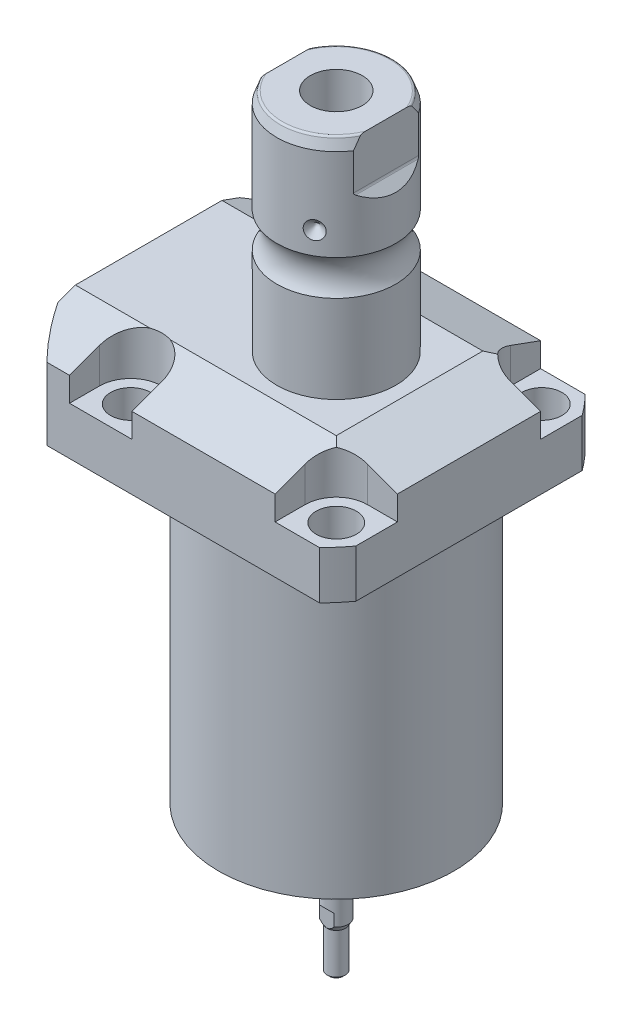
SolidWorks part; units mm, degrees
material "Alloy Steel"
ref_plane "Front Plane" through (0, 0, 0) normal (0, 0, 1) x (1, 0, 0)
ref_plane "Top Plane" through (0, 0, 0) normal (0, 1, 0) x (1, 0, 0)
ref_plane "Right Plane" through (0, 0, 0) normal (1, 0, 0) x (0, 0, -1)
sketch "Sketch1" plane through (0, 0, 0) normal (0, -1, 0) x (0, 0, 1)
  line L0 (-35.433, 50.063) -> (35.433, 50.063)
  line L1 (35.433, 50.063) -> (35.433, -35.433)
  line L2 (35.433, -35.433) -> (-35.433, -35.433)
  line L3 (-35.433, -35.433) -> (-35.433, 50.063)
  line L4 (0, 0) -> (0, -60.6467) construction
  dimension "D1" = 35.433
  dimension "D2" = 85.496
  dimension "D3" = 70.866
extrude "Extrude1" add sketch "Sketch1" against normal blind 104.521
sketch "Sketch2" plane through (0, 0, 0) normal (0, -1, 0) x (1, 0, 0)
  circle A0 centre (-5.4102, 0) radius 50.8
  dimension "D1" = 101.6
  dimension "D2" = 5.4102
extrude "Cut-Extrude1" cut sketch "Sketch2" against normal through all flip side to cut
sketch "Sketch3" plane through (0, 0, 0) normal (1, 0, 0) x (0, 0, -1)
  line L0 (31.3945, 0) -> (31.3945, 79.502)
  line L1 (31.3945, 79.502) -> (76.5937, 79.502)
  line L2 (76.5937, 79.502) -> (76.5937, 0)
  line L3 (76.5937, 0) -> (31.3945, 0)
  line L4 (0, -93.345) -> (0, 4.445) construction
  line L5 (24.2233, 0) -> (-24.2233, 0) construction
  dimension "D1" = 62.789
  dimension "D2" = 153.1874
  dimension "D3" = 79.502
revolve "Cut-Revolve1" cut sketch "Sketch3" angle 360 about L4
fillet "Fillet1" radius 0.381 1 edges at (0, 79.502, -31.3945)
sketch "Sketch4" plane through (0, 104.521, 0) normal (0, 1, 0) x (-1, 0, 0)
  line L0 (-35.433, -30.2072) -> (-35.433, 30.2072) construction
  line L1 (41.8127, 35.433) -> (-30.9923, 35.433) construction
  line L2 (-19.1008, -35.433) -> (-19.1008, -27.432)
  line L3 (-35.433, -35.433) -> (-19.1008, -35.433)
  line L4 (-35.433, -19.1008) -> (-35.433, -35.433)
  line L5 (-27.432, -19.1008) -> (-35.433, -19.1008)
  line L6 (35.7632, -35.433) -> (19.1008, -35.433)
  line L7 (19.1008, 35.433) -> (19.1008, 27.432)
  line L8 (35.7632, 35.433) -> (35.7632, 27.432)
  line L9 (35.7632, 35.433) -> (19.1008, 35.433)
  line L10 (-27.432, 19.1008) -> (-35.433, 19.1008)
  line L11 (-35.433, 19.1008) -> (-35.433, 35.433)
  line L12 (-35.433, 35.433) -> (-19.1008, 35.433)
  line L13 (-19.1008, 35.433) -> (-19.1008, 27.432)
  line L14 (-48.9217, 0) -> (49.4551, 0) construction
  line L15 (35.7632, -35.433) -> (35.7632, -27.432)
  line L16 (19.1008, -35.433) -> (19.1008, -27.432)
  arc A0 (19.1008, -27.432) -> (35.7632, -27.432) centre (27.432, -27.432) cw
  arc A1 (-27.432, -19.1008) -> (-19.1008, -27.432) centre (-27.432, -27.432) cw
  arc A2 (-27.432, 19.1008) -> (-19.1008, 27.432) centre (-27.432, 27.432) ccw
  arc A3 (19.1008, 27.432) -> (35.7632, 27.432) centre (27.432, 27.432) ccw
  dimension "D2" = 8.3312
  dimension "D1" = 27.432
  dimension "D3" = 27.432
  dimension "D4" = 54.864
extrude "Cut-Extrude2" cut sketch "Sketch4" against normal blind 12.243
sketch "Sketch5" plane through (0, 0, 0) normal (1, 0, 0) x (0, 0, -1)
  line L0 (-19.558, 104.521) -> (-35.433, 98.743)
  line L1 (0, 0) -> (0, 154.1081) construction
  line L2 (-19.558, 104.521) -> (-35.433, 104.521)
  line L3 (-35.433, 104.521) -> (-35.433, 98.743)
  dimension "D1" = 15.875
  dimension "D2" = 20
extrude "Cut-Extrude9" cut sketch "Sketch5" against normal through all and the other way through all
mirror "Mirror1" about plane through (0, 0, 0) normal (0, 0, 1) of "Cut-Extrude9"
sketch "Sketch9" plane through (0, 0, 0) normal (0, 0, 1) x (1, 0, 0)
  line L0 (19.558, 104.521) -> (35.433, 98.743)
  line L1 (35.433, 98.743) -> (35.433, 104.521)
  line L2 (35.433, 104.521) -> (19.558, 104.521)
  dimension "D1" = 15.875
  dimension "D2" = 20
extrude "Cut-Extrude7" cut sketch "Sketch9" against normal through all and the other way through all
ref_plane "Plane14" through (-35.0774, 0, 0) normal (1, 0, 0) x (0, 0, -1)
sketch "Sketch20" plane through (-35.0774, 88.9, -18.1102) normal (1, 0, 0) x (0, 1, 0)
  line L0 (-88.9, 18.1102) -> (39.8401, 18.1102) construction
  line L1 (-7.2797, 32.639) -> (36.9042, 32.639) construction
  line L2 (-9.398, 38.3413) -> (-7.9502, 38.3413)
  line L3 (-9.398, -6.1131) -> (-9.398, 42.3335) construction
  line L4 (-7.9502, 38.3413) -> (-7.9502, 35.8902)
  line L5 (-7.9502, 35.8902) -> (-6.9342, 35.8902)
  line L6 (-6.9342, 35.8902) -> (-6.9342, 33.8836)
  line L7 (-6.9342, 33.8836) -> (4.0386, 33.8836)
  line L8 (4.0386, 33.8836) -> (4.0386, 32.639)
  line L9 (4.0386, 32.639) -> (-9.398, 32.639)
  line L10 (-9.398, 38.3413) -> (-9.398, 32.639)
  dimension "D1" = 14.5288
  dimension "D2" = 11.4046
  dimension "D3" = 1.4478
  dimension "D4" = 6.5024
  dimension "D5" = 1.016
  dimension "D6" = 2.4892
  dimension "D7" = 10.9728
revolve "Cut-Revolve4" cut sketch "Sketch20" angle 360 about L1
mirror "Mirror10" about plane through (0, 0, 0) normal (0, 0, 1) of "Cut-Revolve4"
sketch "Sketch10" plane through (-35.0774, 88.9, -18.1102) normal (1, 0, 0) x (0, 1, 0)
  line L0 (-1.0325, 3.5814) -> (1.5659, 3.5814) construction
  line L1 (4.0386, 4.826) -> (-6.9342, 4.826) construction
  line L2 (-6.9342, 2.3368) -> (4.0386, 2.3368) construction
  line L4 (-9.398, -12.097) -> (-9.398, 48.3174) construction
  circle A0 centre (-9.1313, 8.1026) radius 1.1811
  dimension "D1" = 2.3622
  dimension "D2" = 0.2667
  dimension "D3" = 9.0424
revolve "Revolve4" add sketch "Sketch10" angle 360 about L0
mirror "Mirror12" about plane through (0, 0, 0) normal (0, 0, 1) of bodies 135
sketch "Sketch15" plane through (0, 0, 0) normal (1, 0, 0) x (0, 0, -1)
  line L0 (0, 104.521) -> (15.875, 104.521)
  line L1 (15.875, 104.521) -> (15.875, 127.9059)
  line L2 (15.875, 137.3201) -> (15.875, 161.798)
  line L3 (14.8118, 164.719) -> (0, 164.719)
  line L4 (0, 164.719) -> (0, 104.521)
  line L5 (0, 250.2908) -> (0, 28.9095) construction
  line L6 (19.558, 104.521) -> (-19.558, 104.521) construction
  line L7 (14.8118, 164.719) -> (15.875, 161.798)
  line L8 (-31.3945, 0) -> (31.3945, 0) construction
  arc A0 (15.875, 137.3201) -> (15.875, 127.9059) centre (22.2504, 132.613) ccw
  dimension "D2" = 20
  dimension "D4" = 7.9248
  dimension "D6" = 28.6512
  dimension "D1" = 164.719
  dimension "D3" = 31.75
  dimension "D5" = 32.106
  dimension "D7" = 2.921
revolve "Revolve3" add sketch "Sketch15" angle 360 about L5
hole_wizard "Hole1" positions "Sketch18" profile "Sketch17" legacy end condition up to next
sketch "Sketch18" plane through (0, 92.278, 0) normal (0, 1, 0) x (-1, 0, 0)
  arc A0 (35.7632, -27.432) -> (19.1008, -27.432) centre (27.432, -27.432) ccw construction
  arc A1 (19.1008, 27.432) -> (35.7632, 27.432) centre (27.432, 27.432) ccw construction
  arc A2 (-27.432, 19.1008) -> (-19.1008, 27.432) centre (-27.432, 27.432) ccw construction
  arc A3 (-19.1008, -27.432) -> (-27.432, -19.1008) centre (-27.432, -27.432) ccw construction
  point P0 (-27.432, -27.432)
  point P1 (-27.432, 27.432)
  point P3 (27.432, 27.432)
  point P5 (27.432, -27.432)
sketch "Sketch17" plane through (27.432, 92.278, -27.432) normal (1, 0, 0) x (0, 0, 1)
  line L0 (0, 0) -> (0, 12.776)
  line L1 (0, 12.776) -> (5.3594, 12.776)
  line L2 (5.3594, 12.776) -> (5.3594, 0)
  line L3 (5.3594, 0) -> (0, 0)
  line L4 (0, 110) -> (0, -10) construction
  dimension "Diameter" = 10.7188
  dimension "Depth" = 12.776
chamfer "Chamfer1" distance 0.635 angle 45 2 edges at (-35.0774, 81.9658, 13.2842) (-35.0774, 81.9658, -13.2842)
ref_plane "Plane15" through (0, 92.5068, 0) normal (0, -1, 0) x (1, 0, 0)
sketch "Sketch21" plane through (0, 92.5068, 0) normal (0, -1, 0) x (1, 0, 0)
  line L0 (-57.5495, -12.9794) -> (-2.9353, -12.9794) construction
  line L1 (-50.063, -1.9304) -> (-49.809, -1.9304)
  line L2 (-49.809, -1.9304) -> (-49.809, -6.3246)
  line L3 (-49.809, -6.3246) -> (-49.0978, -7.0358)
  line L4 (-49.0978, -7.0358) -> (-35.6358, -7.0358)
  line L5 (-35.6358, -7.0358) -> (-35.6358, -12.9794)
  line L6 (-35.6358, -12.9794) -> (-50.063, -12.9794)
  line L7 (-50.063, 24.2233) -> (-50.063, -24.2233) construction
  line L8 (-50.063, -12.9794) -> (-50.063, -1.9304)
  dimension "D1" = 12.9794
  dimension "D2" = 0.254
  dimension "D3" = 22.098
  dimension "D4" = 45
  dimension "D5" = 0.7112
  dimension "D6" = 11.8872
  dimension "D7" = 14.1732
revolve "Cut-Revolve5" cut sketch "Sketch21" angle 360 about L0
mirror "Mirror13" about plane through (0, 0, 0) normal (0, 0, 1) of "Cut-Revolve5"
fillet "Fillet2" radius 0.635 1 edges at (0, 164.719, 14.8118)
sketch "Sketch26" plane through (0, 0, 0) normal (0, 0, 1) x (1, 0, 0)
  line L0 (-39.772, 143.301) -> (35.3173, 143.301) construction
  line L1 (-15.875, 145.714) -> (-13.462, 143.301)
  line L2 (-15.875, 161.798) -> (-15.875, 137.3201) construction
  line L3 (-13.462, 143.301) -> (-15.875, 143.301)
  line L4 (-15.875, 143.301) -> (-15.875, 145.714)
  arc A0 (-15.875, 127.9059) -> (-15.875, 137.3201) centre (-22.2504, 132.613) ccw construction
  dimension "D1" = 45
  dimension "D2" = 4.826
  dimension "D3" = 10.688
revolve "Cut-Revolve7" cut sketch "Sketch26" angle 360 about L0
pattern_circular "CirPattern1" count 3 over 360 about axis through (0, 250.2908, 0) along (0, 1, 0) of "Cut-Revolve7"
hole_wizard "Hole2" positions "Sketch28" profile "Sketch27" legacy
sketch "Sketch28" plane through (0, 164.719, 0) normal (0, 1, 0) x (-1, 0, 0)
  circle A0 centre (0, 0) radius 15.875 construction
  point P0 (0, 0)
sketch "Sketch27" plane through (0, 164.719, 0) normal (1, 0, 0) x (0, 0, 1)
  line L0 (0, 0) -> (0, 29.5665)
  line L1 (0, 29.5665) -> (6.9342, 25.4)
  line L2 (6.9342, 25.4) -> (6.9342, 0)
  line L4 (6.9342, 0) -> (0, 0)
  line L6 (0, 29.5665) -> (-6.9342, 25.4) construction
  line L7 (0, -4.2442) -> (0, 117.3081) construction
  dimension "Diameter" = 13.8684
  dimension "Depth" = 25.4
  dimension "Drill Angle" = 118
sketch "Sketch29" plane through (0, 0, 0) normal (0, 0, 1) x (1, 0, 0)
  line L0 (0, 0) -> (0, 192.0172) construction
  line L1 (13.284, 164.719) -> (13.284, 152.019)
  line L2 (14.3672, 164.719) -> (-14.3672, 164.719) construction
  line L3 (13.5072, 151.4802) -> (15.875, 149.1124)
  line L5 (15.875, 149.1124) -> (15.875, 164.719)
  line L6 (15.875, 164.719) -> (13.284, 164.719)
  line L7 (-15.875, 164.719) -> (-13.284, 164.719)
  line L8 (-15.875, 149.1124) -> (-15.875, 164.719)
  line L9 (-13.5072, 151.4802) -> (-15.875, 149.1124)
  line L10 (-13.284, 164.719) -> (-13.284, 152.019)
  arc A0 (13.284, 152.019) -> (13.5072, 151.4802) centre (14.046, 152.019) ccw
  arc A1 (-13.284, 152.019) -> (-13.5072, 151.4802) centre (-14.046, 152.019) cw
  dimension "D2" = 0.762
  dimension "D1" = 45
  dimension "D3" = 26.568
  dimension "D4" = 12.7
extrude "Cut-Extrude10" cut sketch "Sketch29" against normal through all and the other way through all
sketch "Sketch30" plane through (0, 0, 0) normal (1, 0, 0) x (0, 0, -1)
  line L0 (0, -1000) -> (0, 49000) construction
  line L1 (0, 0) -> (3.175, 0)
  line L2 (-31.3945, 0) -> (31.3945, 0) construction
  line L3 (3.175, 0) -> (3.175, -26.4106)
  line L4 (3.175, -26.4106) -> (2.4384, -27.6864)
  line L5 (2.4384, -27.6864) -> (2.4384, -38.4814)
  line L6 (2.4384, -38.4814) -> (1.8034, -39.1164)
  line L7 (1.8034, -39.1164) -> (0, -39.1164)
  line L8 (0, -39.1164) -> (0, 0)
  line L9 (-5.4728, 164.719) -> (-14.3672, 164.719) construction
  dimension "D1" = 45
  dimension "D2" = 0.635
  dimension "D3" = 4.8768
  dimension "D4" = 30
  dimension "D5" = 6.35
  dimension "D6" = 11.43
  dimension "D7" = 203.8354
revolve "Revolve5" add sketch "Sketch30" angle 360 about L0
sketch "Sketch33" plane through (0, 0, 0) normal (1, 0, 0) x (0, 0, -1)
  line L0 (0, -1000) -> (0, 49000) construction
  line L1 (2.5019, -39.1164) -> (2.5019, -23.2414)
  line L2 (-1.8034, -39.1164) -> (1.8034, -39.1164) construction
  line L3 (2.5019, -23.2414) -> (3.175, -22.5683)
  line L4 (3.175, -26.4106) -> (3.175, 0) construction
  line L5 (3.175, -22.5683) -> (3.175, -39.1164)
  line L6 (3.175, -39.1164) -> (2.5019, -39.1164)
  line L7 (-3.175, -39.1164) -> (-2.5019, -39.1164)
  line L8 (-2.5019, -39.1164) -> (-2.5019, -23.2414)
  line L9 (-3.175, -22.5683) -> (-3.175, -39.1164)
  line L10 (-2.5019, -23.2414) -> (-3.175, -22.5683)
  dimension "D1" = 5.0038
  dimension "D2" = 15.875
  dimension "D3" = 45
extrude "Cut-Extrude11" cut sketch "Sketch33" against normal mid plane 7.62
sketch "Sketch34" plane through (0, 0, 0) normal (1, 0, 0) x (0, 0, -1)
  line L0 (0, -1000) -> (0, 49000) construction
  line L1 (-31.3945, 0) -> (31.3945, 0) construction
  line L2 (11.6459, 0) -> (14.351, 0)
  line L3 (11.6459, 0) -> (11.6459, 1.3208)
  line L4 (11.6459, 1.3208) -> (14.351, 1.3208)
  line L5 (14.351, 0) -> (14.351, 1.3208)
  dimension "D1" = 23.2918
  dimension "D2" = 28.7021
  dimension "D3" = 1.3208
revolve "Cut-Revolve8" cut sketch "Sketch34" angle 360 about L0
sketch "Sketch35" plane through (0, 0, 0) normal (0, -1, 0) x (1, 0, 0)
  line L0 (-1000, 0) -> (49000, 0) construction
  line L1 (0, 0) -> (48296.2913, -12940.9523) construction
  line L2 (0, 0) -> (25000, 43301.2702) construction
  circle A0 centre (0, 0) radius 19.431 construction
  circle A1 centre (19.431, 0) radius 1.27
  circle A2 centre (18.7689, -5.0291) radius 1.27
  circle A3 centre (-13.7398, 13.7398) radius 1.27
  circle A4 centre (-9.7155, 16.8278) radius 1.27
  circle A5 centre (-13.7398, -13.7398) radius 1.27
  circle A6 centre (-9.7155, -16.8278) radius 1.27
  dimension "D3" = 38.8621
  dimension "D4" = 2.54
  dimension "D5" = 2.54
  dimension "D1" = 15
  dimension "D2" = 60
extrude "Cut-Extrude12" cut sketch "Sketch35" against normal blind 7.62
